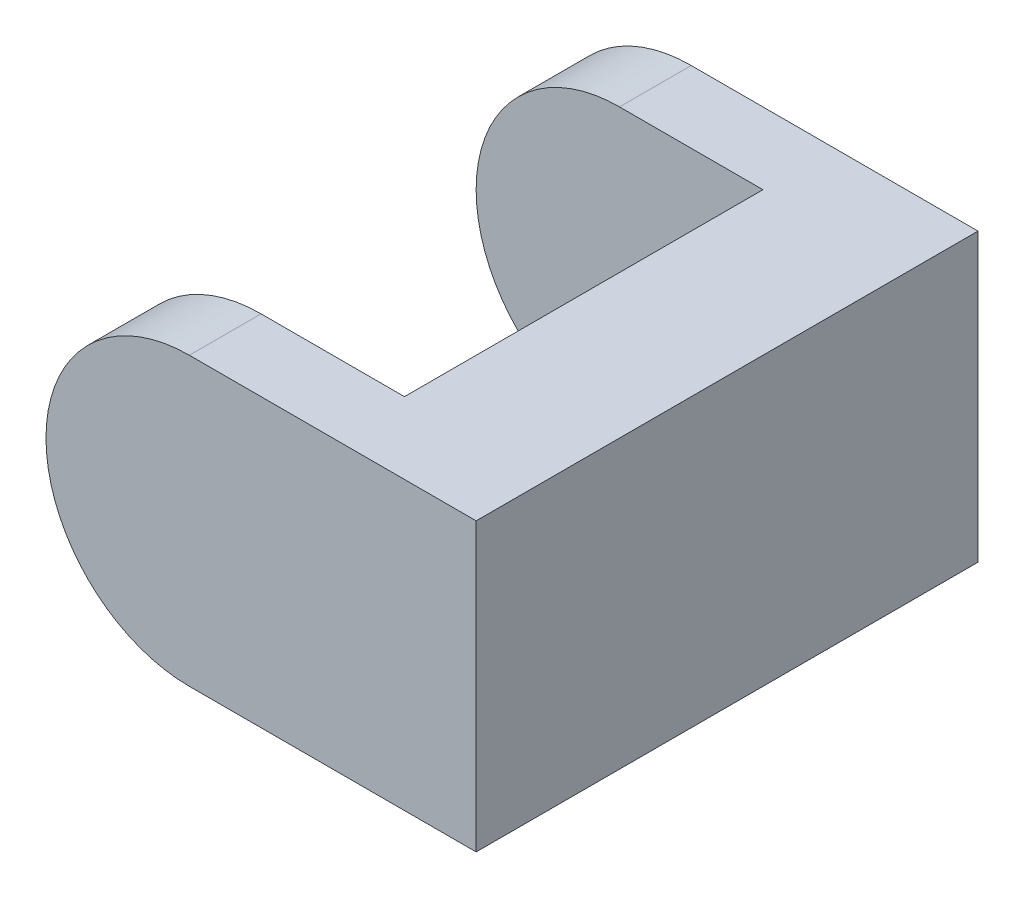
SolidWorks part; units mm, degrees
ref_plane "Piano frontale" through (0, 0, 0) normal (0, 0, 1) x (1, 0, 0)
ref_plane "Piano superiore" through (0, 0, 0) normal (0, 1, 0) x (1, 0, 0)
ref_plane "Piano destro" through (0, 0, 0) normal (1, 0, 0) x (0, 0, -1)
sketch "Schizzo1" plane through (0, 0, 0) normal (0, 0, 1) x (1, 0, 0)
  line L1 (40, 40) -> (-40, 40)
  line L2 (40, 40) -> (40, -40)
  line L3 (40, -40) -> (-40, -40)
  line L5 (40, 40) -> (-40, -40) construction
  line L6 (40, -40) -> (-40, 40) construction
  arc A0 (-40, 40) -> (-40, -40) centre (-40, 0) ccw
  point P0 (0, 0)
  dimension "D1" = 80
  dimension "D2" = 80
extrude "Estrusione-Estrusione1" add sketch "Schizzo1" along normal blind 140
sketch "Schizzo2" plane through (0, 40, 0) normal (0, 1, 0) x (1, 0, 0)
  line L0 (-80, 0) -> (-80, -140) construction
  line L1 (-160, -20) -> (0, -20)
  line L2 (-160, -20) -> (-160, -120)
  line L3 (-160, -120) -> (0, -120)
  line L4 (0, -20) -> (0, -120)
  line L5 (-160, -20) -> (0, -120) construction
  line L6 (-160, -120) -> (0, -20) construction
  point P0 (-80, -70)
  dimension "D1" = 100
  dimension "D2" = 160
extrude "Taglio-Estrusione1" cut sketch "Schizzo2" against normal blind 140
